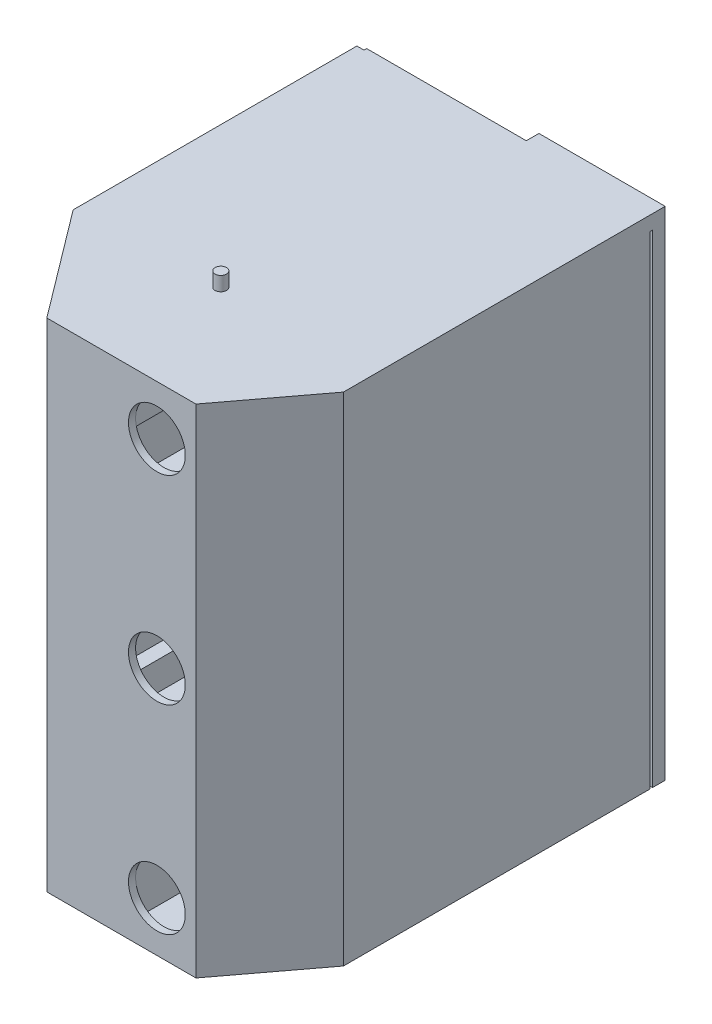
SolidWorks part; units mm, degrees
material "C-Glass Fiber"
ref_plane "Front Plane" through (0, 0, 0) normal (0, 0, 1) x (1, 0, 0)
ref_plane "Top Plane" through (0, 0, 0) normal (0, 1, 0) x (1, 0, 0)
ref_plane "Right Plane" through (0, 0, 0) normal (1, 0, 0) x (0, 0, -1)
sketch "Sketch1" plane through (0, 0, 0) normal (0, 1, 0) x (1, 0, 0)
  line L0 (-50, 0) -> (50, 0)
  line L1 (50, 0) -> (92.1271, 55.9045)
  line L2 (-50, 0) -> (-104.1634, 71.8772)
  line L3 (92.1271, 55.9045) -> (92.1271, 270)
  line L4 (-104.1634, 71.8772) -> (-104.1634, 270)
  point P4 (0, 0)
extrude "Extrude-Thin1" add sketch "Sketch1" along normal blind 350 thin
sketch "Sketch5" plane through (0, 0, 0) normal (0, -1, 0) x (1, 0, 0)
  line L0 (0, 0) -> (0, -250)
extrude "Extrude-Thin3" add sketch "Sketch5" against normal blind 350 thin thin type two direction wall 5 second wall 5
sketch "Sketch8" plane through (5, 0, 0) normal (1, 0, 0) x (0, 0, -1)
  line L0 (0, 350) -> (0, 0) construction
  line L1 (0, 160) -> (150, 160)
  line L2 (0, 160) -> (0, 210)
  line L3 (0, 210) -> (150, 210)
  line L4 (150, 160) -> (150, 210)
  dimension "D1" = 50
extrude "Cut-Extrude2" cut sketch "Sketch8" against normal blind 20
pattern_linear "LPattern4" count 2 spacing 100 along (0, 1, 0) of "Cut-Extrude2"
pattern_linear "LPattern5" count 2 spacing 100 along (0, -1, 0) of "Cut-Extrude2"
sketch "Sketch9" plane through (0, 0, 0) normal (0, -1, 0) x (-1, 0, 0)
  line L0 (104.1634, 270) -> (104.1634, 71.8772)
  line L1 (104.1634, 71.8772) -> (50, 0)
  line L2 (50, 0) -> (-50, 0)
  line L3 (-50, 0) -> (-92.1271, 55.9045)
  line L4 (-92.1271, 55.9045) -> (-92.1271, 270)
  line L5 (-92.1271, 270) -> (104.1634, 270)
extrude "Boss-Extrude1" add sketch "Sketch9" against normal blind 10
sketch "Sketch10" plane through (0, 350, 0) normal (0, 1, 0) x (1, 0, 0)
  line L0 (97.1271, 271.8772) -> (97.1271, 54.2315)
  line L1 (97.1271, 54.2315) -> (50, 0)
  line L2 (50, 0) -> (-50, 0)
  line L3 (-50, 0) -> (-104.1634, 71.8772)
  line L4 (-104.1634, 71.8772) -> (-104.1634, 271.8772)
  line L5 (-104.1634, 271.8772) -> (97.1271, 271.8772)
extrude "Boss-Extrude2" add sketch "Sketch10" against normal blind 10
sketch "Sketch12" plane through (0, 0, 0) normal (0, 0, -1) x (-1, 0, 0)
  circle A0 centre (-25, 35) radius 20
  circle A1 centre (-25, 175) radius 20
  circle A2 centre (-25, 315) radius 20
extrude "Cut-Extrude3" cut sketch "Sketch12" against normal blind 5
sketch "Sketch13" plane through (0, 0, 0) normal (0, 0, -1) x (-1, 0, 0)
  line L0 (-5, 135) -> (-50, 135)
  line L1 (-5, 160) -> (-5, 110) construction
extrude "Extrude-Thin4" add sketch "Sketch13" along normal blind 45 thin
sketch "Sketch15" plane through (0, 140, 0) normal (0, 1, 0) x (1, 0, 0)
  line L0 (50, 0) -> (50, 45)
  line L1 (50, 45) -> (85.7451, 45)
  line L2 (50, 0) -> (85.7451, 45)
extrude "Boss-Extrude4" add sketch "Sketch15" against normal blind 5
pattern_linear "LPattern6" count 2 spacing 140 along (0, 1, 0) of "Extrude-Thin4", "Boss-Extrude4"
sketch "Sketch16" plane through (0, 350, 0) normal (0, 1, 0) x (1, 0, 0)
  circle A0 centre (-10, 75) radius 4
extrude "Boss-Extrude13" add sketch "Sketch16" against normal blind 380 and the other way blind 10 contours A0
scale "Scale2" scale about centroid uniform scaling yes scale factor 0.5625
sketch "Sketch17" plane through (0, 0, -53.0432) normal (0, 0, 1) x (1, 0, 0)
  point P0 (12.5762, 253.6107)
  point P1 (12.5762, 174.8607)
  point P3 (12.5762, 96.1107)
sketch "Sketch18" plane through (0, 0, -208.7866) normal (0, 0, -1) x (-1, 0, 0)
  line L0 (-53.1476, 273.2982) -> (60.0782, 273.2982) construction
  line L1 (-53.1476, 76.4232) -> (-3.1476, 76.4232)
  line L2 (-53.1476, 76.4232) -> (-53.1476, 273.2982)
  line L3 (-53.1476, 273.2982) -> (-3.1476, 273.2982)
  line L4 (-3.1476, 76.4232) -> (-3.1476, 273.2982)
  dimension "D1" = 50
extrude "Boss-Extrude14" add sketch "Sketch18" along normal blind 5
sketch "Sketch19" plane through (0, 0, -213.7866) normal (0, 0, -1) x (-1, 0, 0)
  text T0 "SEED TANK" font "Century Gothic" height 15
extrude "Cut-Extrude4" cut sketch "Sketch19" against normal blind 1
